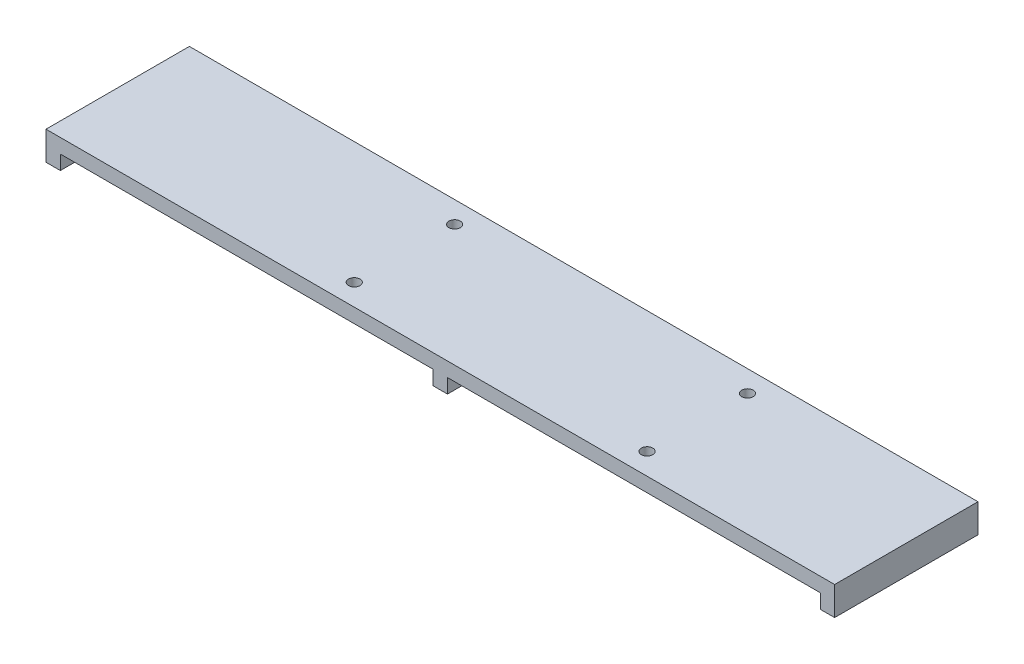
SolidWorks part; units mm, degrees
material "PBT generico"
ref_plane "Piano frontale" through (0, 0, 0) normal (0, 0, 1) x (1, 0, 0)
ref_plane "Piano superiore" through (0, 0, 0) normal (0, 1, 0) x (1, 0, 0)
ref_plane "Piano destro" through (0, 0, 0) normal (1, 0, 0) x (0, 0, -1)
sketch "Schizzo1" plane through (0, 0, 0) normal (0, 1, 0) x (1, 0, 0)
  line L1 (0, 0) -> (550, 0)
  line L2 (0, 0) -> (0, 100)
  line L3 (0, 100) -> (550, 100)
  line L4 (550, 0) -> (550, 100)
  circle A0 centre (200, 85) radius 4
  circle A1 centre (200, 15) radius 4
  circle A2 centre (404.2, 15) radius 4
  circle A3 centre (404.2, 85) radius 4
  dimension "D7" = 8
  dimension "D1" = 204.2
  dimension "D2" = 70
  dimension "D3" = 100
  dimension "D4" = 550
  dimension "D5" = 15
  dimension "D6" = 200
extrude "Estrusione-Estrusione1" add sketch "Schizzo1" along normal blind 10
sketch "Schizzo2" plane through (0, 0, 0) normal (0, -1, 0) x (1, 0, 0)
  line L0 (550, -100) -> (0, -100) construction
  line L1 (0, 0) -> (10, 0)
  line L2 (0, 0) -> (0, -100)
  line L3 (0, -100) -> (10, -100)
  line L4 (10, 0) -> (10, -100)
  line L5 (0, 0) -> (550, 0) construction
  line L6 (550, 0) -> (540, 0)
  line L7 (550, 0) -> (550, -100)
  line L8 (550, -100) -> (540, -100)
  line L9 (540, 0) -> (540, -100)
  line L10 (270, 0) -> (280, 0)
  line L11 (270, 0) -> (270, -100)
  line L12 (270, -100) -> (280, -100)
  line L13 (280, 0) -> (280, -100)
  line L14 (275, -127.6944) -> (275, 19.669) construction
  dimension "D1" = 10
  dimension "D2" = 10
  dimension "D3" = 10
extrude "Estrusione-Estrusione2" add sketch "Schizzo2" along normal blind 10
